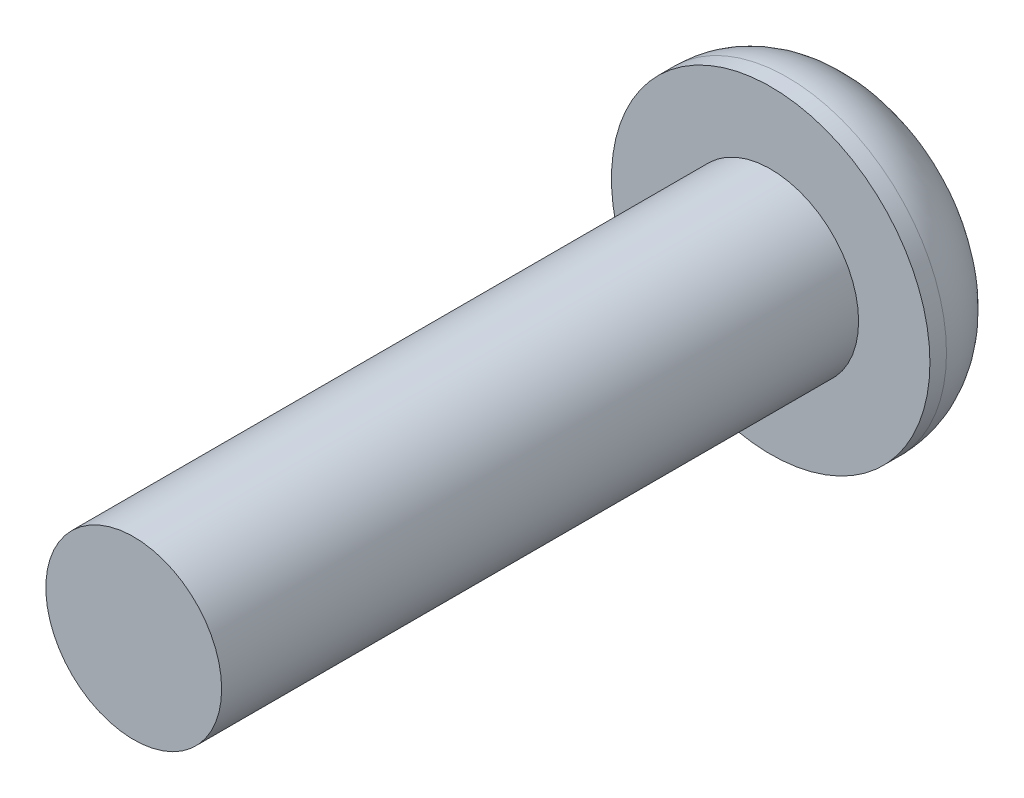
SolidWorks part; units mm, degrees
ref_plane "Front Plane" through (0, 0, 0) normal (0, 0, 1) x (1, 0, 0)
ref_plane "Top Plane" through (0, 0, 0) normal (0, 1, 0) x (1, 0, 0)
ref_plane "Right Plane" through (0, 0, 0) normal (1, 0, 0) x (0, 0, -1)
sketch "Sketch1" plane through (0, 0, 0) normal (0, 0, 1) x (1, 0, 0)
  circle A0 centre (0, 0) radius 3.175
  dimension "D1" = 6.35
extrude "Extrude1" add sketch "Sketch1" along normal blind 1.8542
fillet "Fillet1" radius 1.524 1 edges at (3.175, 0, 0)
sketch "Sketch2" plane through (0, 0, 1.8542) normal (0, 0, 1) x (1, 0, 0)
  circle A0 centre (0, 0) radius 1.7526
  dimension "D1" = 3.5052
extrude "Extrude2" add sketch "Sketch2" along normal blind 12.7
sketch "Sketch3" plane through (0, 0, 0) normal (0, 0, -1) x (-1, 0, 0)
  line L1 (0.5909, 0.9816) -> (-0.5546, 1.0025)
  line L3 (-0.5546, 1.0025) -> (-1.1455, 0.0209)
  line L5 (-1.1455, 0.0209) -> (-0.5909, -0.9816)
  line L6 (-0.5909, -0.9816) -> (0.5546, -1.0025)
  line L7 (0.5546, -1.0025) -> (1.1455, -0.0209)
  line L8 (1.1455, -0.0209) -> (0.5909, 0.9816)
  circle A1 centre (0, 0) radius 0.9922 construction
  point P0 (0, 0)
  point P8 (0, 0)
extrude "Extrude3" cut sketch "Sketch3" against normal blind 1.016
